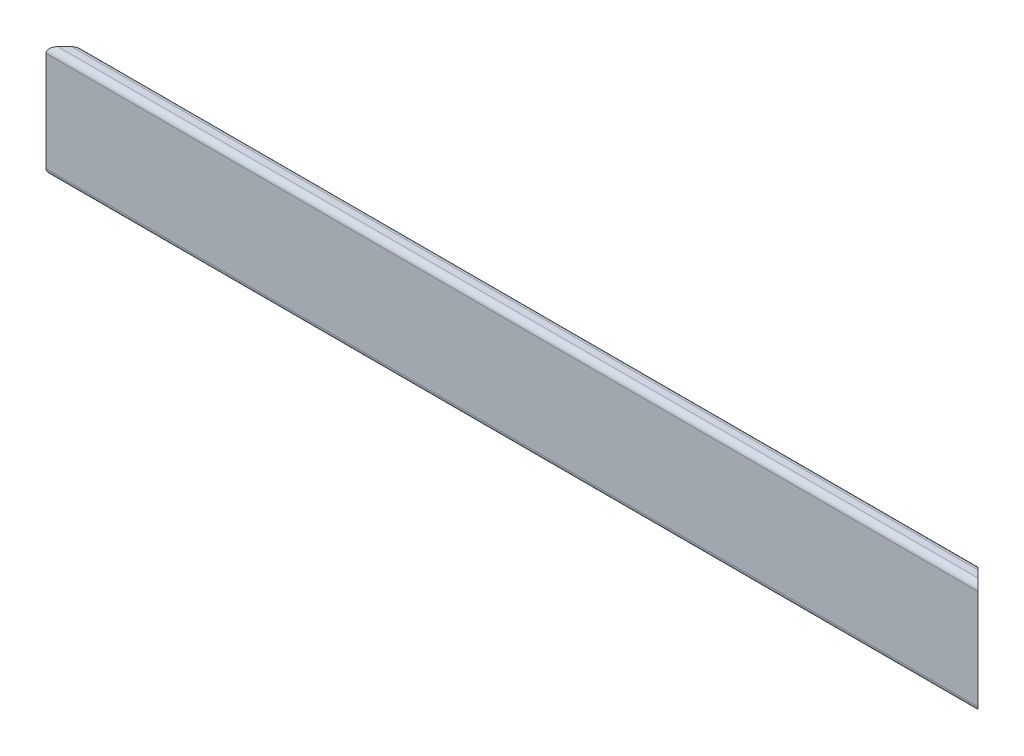
SolidWorks part; units mm, degrees
ref_plane "Front Plane" through (0, 0, 0) normal (0, 0, 1) x (1, 0, 0)
ref_plane "Top Plane" through (0, 0, 0) normal (0, 1, 0) x (1, 0, 0)
ref_plane "Right Plane" through (0, 0, 0) normal (1, 0, 0) x (0, 0, -1)
sketch "Sketch1" plane through (0, 0, 0) normal (0, 1, 0) x (1, 0, 0)
  line L0 (-153, 0) -> (153, 0)
  line L1 (153, 0) -> (159.35, -6.35)
  line L2 (159.35, -6.35) -> (-159.35, -6.35)
  line L3 (-159.35, -6.35) -> (-153, 0)
  point P2 (0, 0)
  dimension "D1" = 45
  dimension "D2" = 45
  dimension "D3" = 6.35
  dimension "D4" = 306
extrude "Boss-Extrude1" add sketch "Sketch1" along normal mid plane 38.1
fillet "Fillet1" radius 2 3 edges at (0, -19.05, 6.35) (0, 19.05, 6.35) (0, 19.05, 0)
equation "\"D3@Sketch1\"=0.25in"
equation "\"D1@Boss-Extrude1\"=1.5in"
